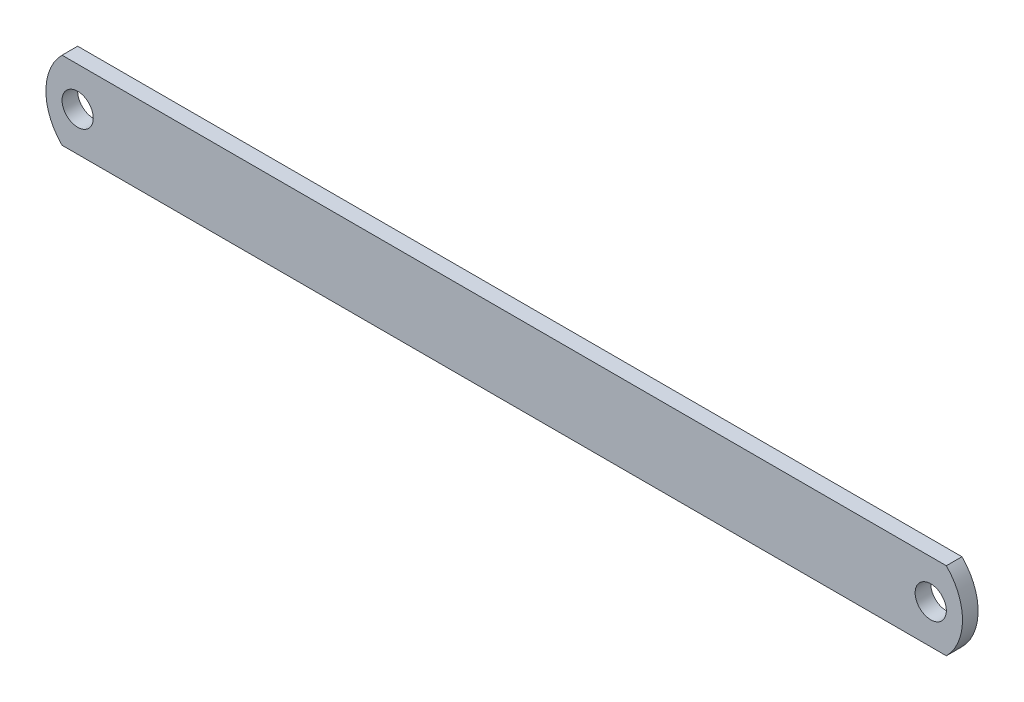
SolidWorks part; units mm, degrees
ref_plane "Front Plane" through (0, 0, 0) normal (0, 0, 1) x (1, 0, 0)
ref_plane "Top Plane" through (0, 0, 0) normal (0, 1, 0) x (1, 0, 0)
ref_plane "Right Plane" through (0, 0, 0) normal (1, 0, 0) x (0, 0, -1)
sketch "Sketch1" plane through (0, 0, 0) normal (0, 0, 1) x (1, 0, 0)
  line L0 (0, 0) -> (170, 0)
  line L2 (0, -15) -> (170, -15)
  arc A0 (170, 0) -> (170, -15) centre (162.5, -7.5) cw
  arc A1 (0, 0) -> (0, -15) centre (7.5, -7.5) ccw
  dimension "D1" = 170
  dimension "D2" = 15
extrude "Boss-Extrude1" add sketch "Sketch1" along normal blind 3
sketch "Sketch2" plane through (0, 0, 3) normal (0, 0, 1) x (1, 0, 0)
  line L0 (0, 0) -> (0, -15)
  line L1 (0, -15) -> (0, -7.5)
  line L2 (0, -7.5) -> (3, -7.5)
  circle A0 centre (3, -7.5) radius 3
  dimension "D1" = 3
extrude "Cut-Extrude1" cut sketch "Sketch2" against normal blind 10 contours A0
sketch "Sketch3" plane through (0, 0, 3) normal (0, 0, 1) x (1, 0, 0)
  line L0 (170, 0) -> (170, -15)
  line L1 (170, -15) -> (170, -7.5)
  line L2 (170, -7.5) -> (167, -7.5)
  circle A0 centre (167, -7.5) radius 3
  dimension "D1" = 3
extrude "Cut-Extrude2" cut sketch "Sketch3" against normal blind 10 contours A0
